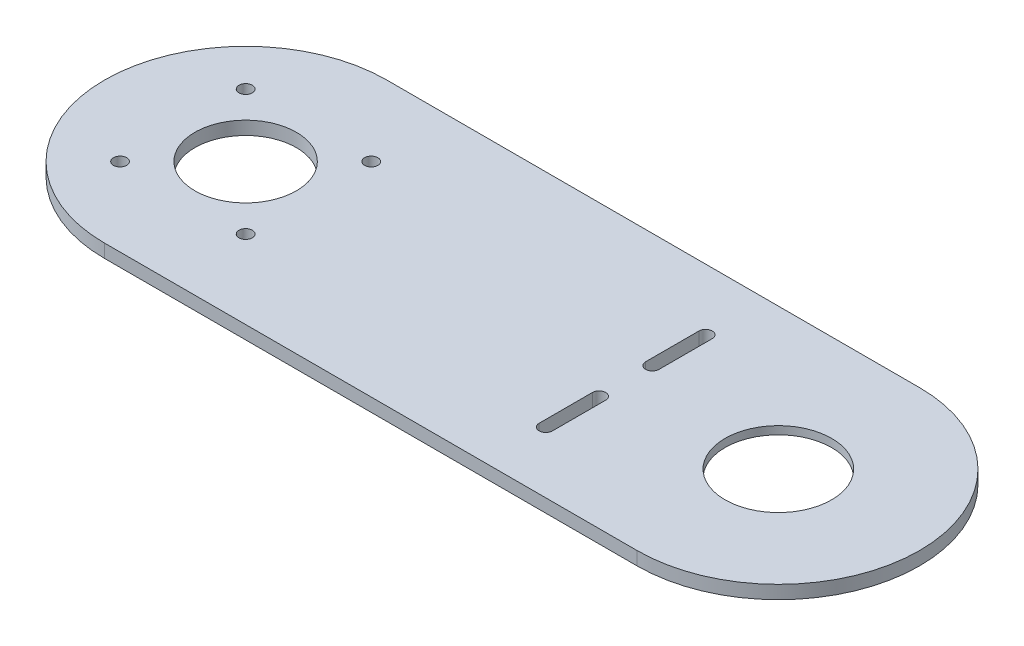
SolidWorks part; units mm, degrees
ref_plane "Front Plane" through (0, 0, 0) normal (0, 0, 1) x (1, 0, 0)
ref_plane "Top Plane" through (0, 0, 0) normal (0, 1, 0) x (1, 0, 0)
ref_plane "Right Plane" through (0, 0, 0) normal (1, 0, 0) x (0, 0, -1)
sketch "Sketch1" plane through (0, 0, 0) normal (0, 1, 0) x (1, 0, 0)
  line L1 (-100, -53) -> (100, -53)
  line L2 (-100, -53) -> (-100, 53)
  line L3 (-100, 53) -> (100, 53)
  line L4 (100, -53) -> (100, 53)
  line L5 (-100, -53) -> (100, 53) construction
  line L6 (-100, 53) -> (100, -53) construction
  circle A0 centre (-100, 0) radius 53
  circle A1 centre (100, 0) radius 53
  point P0 (0, 0)
  dimension "D1" = 200
  dimension "D2" = 106
extrude "Boss-Extrude1" add sketch "Sketch1" along normal blind 5 contours L2 A0 | L2 A0 | A1 L3 A0 L1 | L4 A1 | L4 A1
sketch "Sketch2" plane through (0, 5, 0) normal (0, 1, 0) x (1, 0, 0)
  circle A0 centre (100, 0) radius 20
  dimension "D1" = 40
extrude "Cut-Extrude1" cut sketch "Sketch2" against normal through all
sketch "Sketch3" plane through (0, 0, 0) normal (0, -1, 0) x (1, 0, 0)
  circle A0 centre (100, 0) radius 30
  dimension "D1" = 60
extrude "Cut-Extrude2" cut sketch "Sketch3" against normal blind 2
sketch "Sketch4" plane through (0, 5, 0) normal (0, 1, 0) x (1, 0, 0)
  line L0 (-153, 0) -> (0, 0) construction
  line L1 (0, 0) -> (80, 0) construction
  line L2 (-128.2, 28.2) -> (-71.8, 28.2) construction
  line L3 (-128.2, 28.2) -> (-128.2, -28.2) construction
  line L4 (-128.2, -28.2) -> (-71.8, -28.2) construction
  line L5 (-71.8, 28.2) -> (-71.8, -28.2) construction
  line L6 (-128.2, 28.2) -> (-71.8, -28.2) construction
  line L7 (-128.2, -28.2) -> (-71.8, 28.2) construction
  line L8 (-123.57, 23.57) -> (-76.43, 23.57) construction
  line L9 (-123.57, 23.57) -> (-123.57, -23.57) construction
  line L10 (-123.57, -23.57) -> (-76.43, -23.57) construction
  line L11 (-76.43, 23.57) -> (-76.43, -23.57) construction
  line L12 (-123.57, 23.57) -> (-76.43, -23.57) construction
  line L13 (-123.57, -23.57) -> (-76.43, 23.57) construction
  line L14 (45.1826, 10) -> (45.1826, 30)
  line L15 (40.1826, -10) -> (40.1826, -30)
  line L16 (45.1826, -10) -> (45.1826, -30)
  line L17 (40.1826, 10) -> (40.1826, 30)
  arc A0 (-100, 53) -> (-100, -53) centre (-100, 0) ccw construction
  circle A1 centre (-123.57, 23.57) radius 2.5
  circle A2 centre (-76.43, 23.57) radius 2.5
  circle A3 centre (-76.43, -23.57) radius 2.5
  circle A4 centre (-123.57, -23.57) radius 2.5
  circle A5 centre (-100, 0) radius 19.05
  circle A7 centre (100, 0) radius 20 construction
  arc A8 (45.1826, -10) -> (40.1826, -10) centre (42.6826, -10) ccw
  arc A9 (40.1826, -30) -> (45.1826, -30) centre (42.6826, -30) ccw
  arc A10 (40.1826, 30) -> (45.1826, 30) centre (42.6826, 30) cw
  arc A11 (45.1826, 10) -> (40.1826, 10) centre (42.6826, 10) cw
  point P6 (-100, 0)
  point P11 (-100, 0)
  point P24 (40.1826, -20)
  dimension "D1" = 5
  dimension "D2" = 38.1
  dimension "D8" = 20
  dimension "D9" = 5
  dimension "D3" = 56.4
  dimension "D4" = 56.4
  dimension "D5" = 47.14
  dimension "D6" = 200
  dimension "D7" = 20
extrude "Cut-Extrude3" cut sketch "Sketch4" against normal through all
